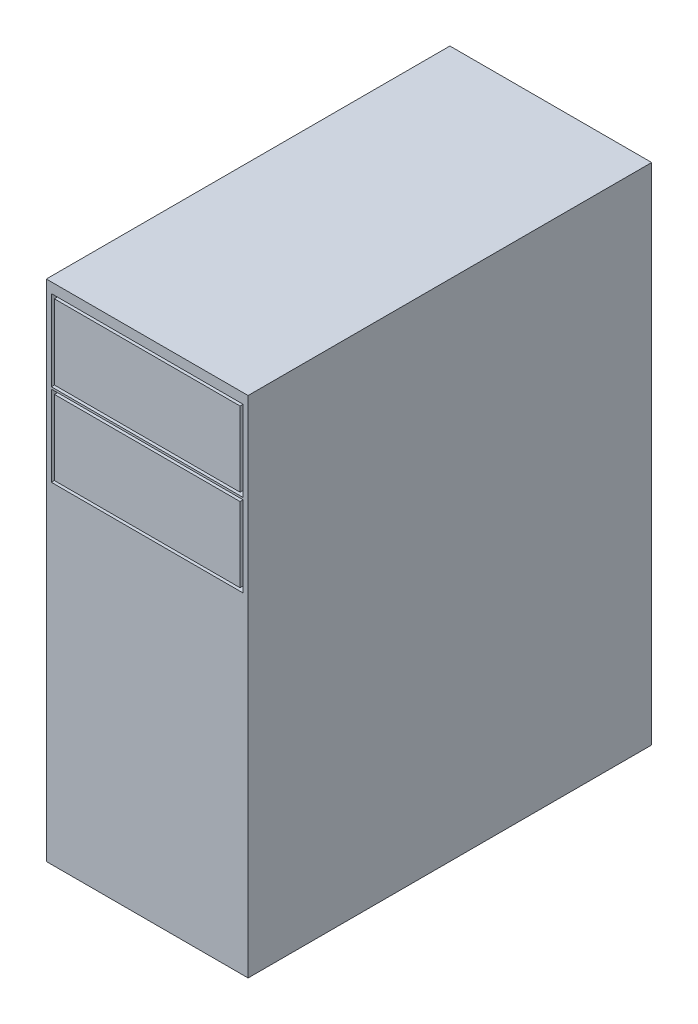
SolidWorks part; units mm, degrees
ref_plane "Front Plane" through (0, 0, 0) normal (0, 0, 1) x (1, 0, 0)
ref_plane "Top Plane" through (0, 0, 0) normal (0, 1, 0) x (1, 0, 0)
ref_plane "Right Plane" through (0, 0, 0) normal (1, 0, 0) x (0, 0, -1)
sketch "Sketch1" plane through (0, 0, 0) normal (0, 1, 0) x (1, 0, 0)
  line L1 (-25, 50) -> (25, 50)
  line L2 (-25, 50) -> (-25, -50)
  line L3 (-25, -50) -> (25, -50)
  line L4 (25, 50) -> (25, -50)
  line L5 (-25, 50) -> (25, -50) construction
  line L6 (-25, -50) -> (25, 50) construction
  point P0 (0, 0)
  dimension "D1" = 50
  dimension "D2" = 100
extrude "Boss-Extrude1" add sketch "Sketch1" along normal blind 125
sketch "Sketch2" plane through (0, 0, 50) normal (0, 0, 1) x (1, 0, 0)
  line L0 (-25, 125) -> (25, 125) construction
  line L1 (-23, 121.75) -> (23, 121.75)
  line L2 (-23, 121.75) -> (-23, 103.25)
  line L3 (-23, 103.25) -> (23, 103.25)
  line L4 (23, 121.75) -> (23, 103.25)
  line L5 (-23, 121.75) -> (23, 103.25) construction
  line L6 (-23, 103.25) -> (23, 121.75) construction
  line L7 (-23.75, 122.5) -> (23.75, 122.5)
  line L8 (-23.75, 122.5) -> (-23.75, 102.5)
  line L9 (-23.75, 102.5) -> (23.75, 102.5)
  line L10 (23.75, 122.5) -> (23.75, 102.5)
  line L11 (-23.75, 122.5) -> (23.75, 102.5) construction
  line L12 (-23.75, 102.5) -> (23.75, 122.5) construction
  line L13 (-23.75, 82) -> (23.75, 82)
  line L14 (-23, 82.75) -> (23, 82.75)
  line L15 (23, 101.25) -> (23, 82.75)
  line L16 (23.75, 102) -> (23.75, 82)
  line L17 (-23, 101.25) -> (23, 101.25)
  line L18 (-23.75, 102) -> (23.75, 102)
  line L19 (-23, 101.25) -> (-23, 82.75)
  line L20 (-23.75, 102) -> (-23.75, 82)
  point P0 (0, 112.5)
  point P5 (0, 112.5)
  dimension "D1" = 0.75
  dimension "D2" = 0.75
  dimension "D3" = 12.5
  dimension "D4" = 20
  dimension "D5" = 47.5
  dimension "D7" = 0.5
  dimension "D6" = 2
extrude "Cut-Extrude1" cut sketch "Sketch2" against normal blind 2
